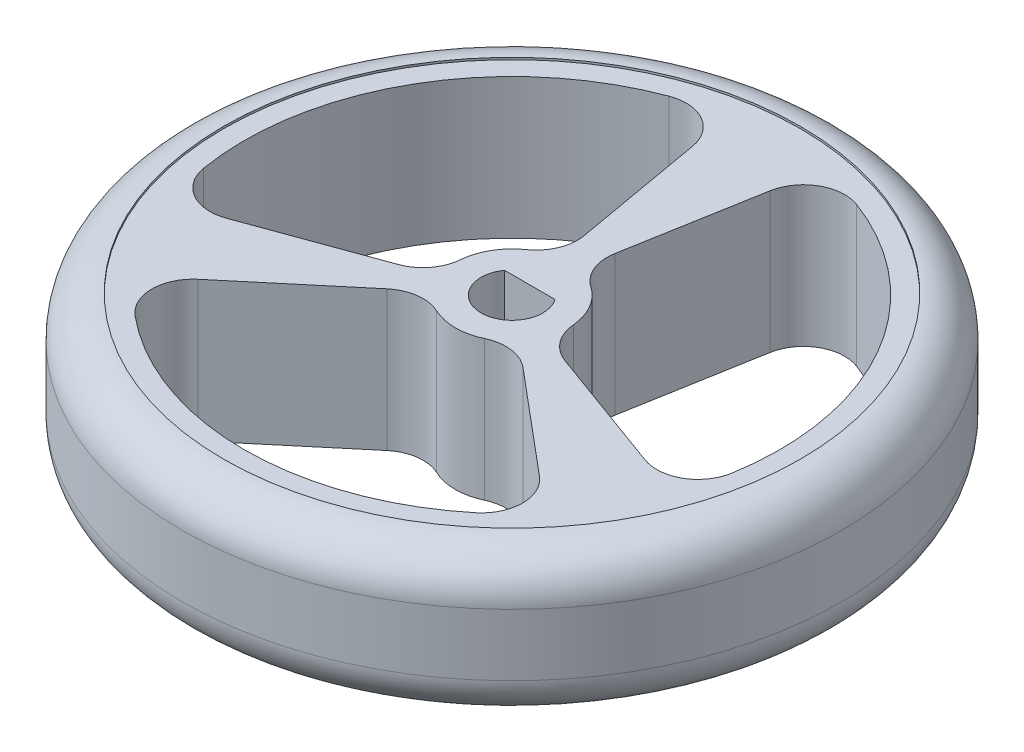
SolidWorks part; units mm, degrees
material "ABS"
ref_plane "Front Plane" through (0, 0, 0) normal (0, 0, 1) x (1, 0, 0)
ref_plane "Top Plane" through (0, 0, 0) normal (0, 1, 0) x (1, 0, 0)
ref_plane "Right Plane" through (0, 0, 0) normal (1, 0, 0) x (0, 0, -1)
sketch "Sketch1" plane through (0, 0, 0) normal (0, 1, 0) x (1, 0, 0)
  line L0 (-1.2272, 0.8625) -> (1.2272, 0.8625)
  line L1 (-0.4775, 2.7082) -> (-2.2574, 12.8025)
  line L2 (0.4775, 2.7082) -> (2.2574, 12.8025)
  line L3 (-0.4775, 2.7082) -> (0, 0) construction
  line L4 (0, 0) -> (0.4775, 2.7082) construction
  line L5 (2.5842, -0.9406) -> (12.216, -4.4463)
  line L6 (2.1066, -1.7677) -> (9.9586, -8.3562)
  line L7 (-2.1066, -1.7677) -> (-9.9586, -8.3562)
  line L8 (-2.5842, -0.9406) -> (-12.216, -4.4463)
  line L9 (0, 0) -> (0, 2.5666) construction
  circle A0 centre (0, 0) radius 16
  arc A1 (-1.2272, 0.8625) -> (1.2272, 0.8625) centre (0, 0) ccw
  circle A2 centre (0, 0) radius 2.75
  circle A3 centre (0, 0) radius 13
  point P20 (0, 0)
  dimension "D1" = 32
  dimension "D2" = 3
  dimension "D4" = 5.5
  dimension "D7" = 3
  dimension "D3" = 0.8625
  dimension "D5" = 20
  dimension "D8" = 10
  dimension "D6" = 3
extrude "Boss-Extrude1" add sketch "Sketch1" along normal mid plane 7 contours A0 A3 | L8 A3 L7 A2 | A2 A1 L0 | L2 A3 L1 A2 | L6 A3 L5 A2
fillet "Fillet2" radius 2 2 edges at (0, 3.5, 16) (0, -3.5, 16)
fillet "Fillet3" radius 2 12 edges at (-0.4775, 0, -2.7082) (-2.5842, 0, 0.9406) (-2.1066, 0, 1.7677) (2.1066, 0, 1.7677) (2.5842, 0, 0.9406) (0.4775, 0, -2.7082) (2.2574, 0, -12.8025) (12.216, 0, 4.4463) (9.9586, 0, 8.3562) (-9.9586, 0, 8.3562) (-12.216, 0, 4.4463) (-2.2574, 0, -12.8025)
sketch "Sketch4" plane through (0, 3.5, 0) normal (0, 1, 0) x (1, 0, 0)
  circle A1 centre (0, 0) radius 14
  circle A2 centre (0, 0) radius 14
  dimension "D1" = 0
extrude "Cut-Extrude2" cut sketch "Sketch4" against normal blind 0.1
mirror "Mirror1" about plane through (0, 0, 0) normal (0, 1, 0) of "Cut-Extrude2"
